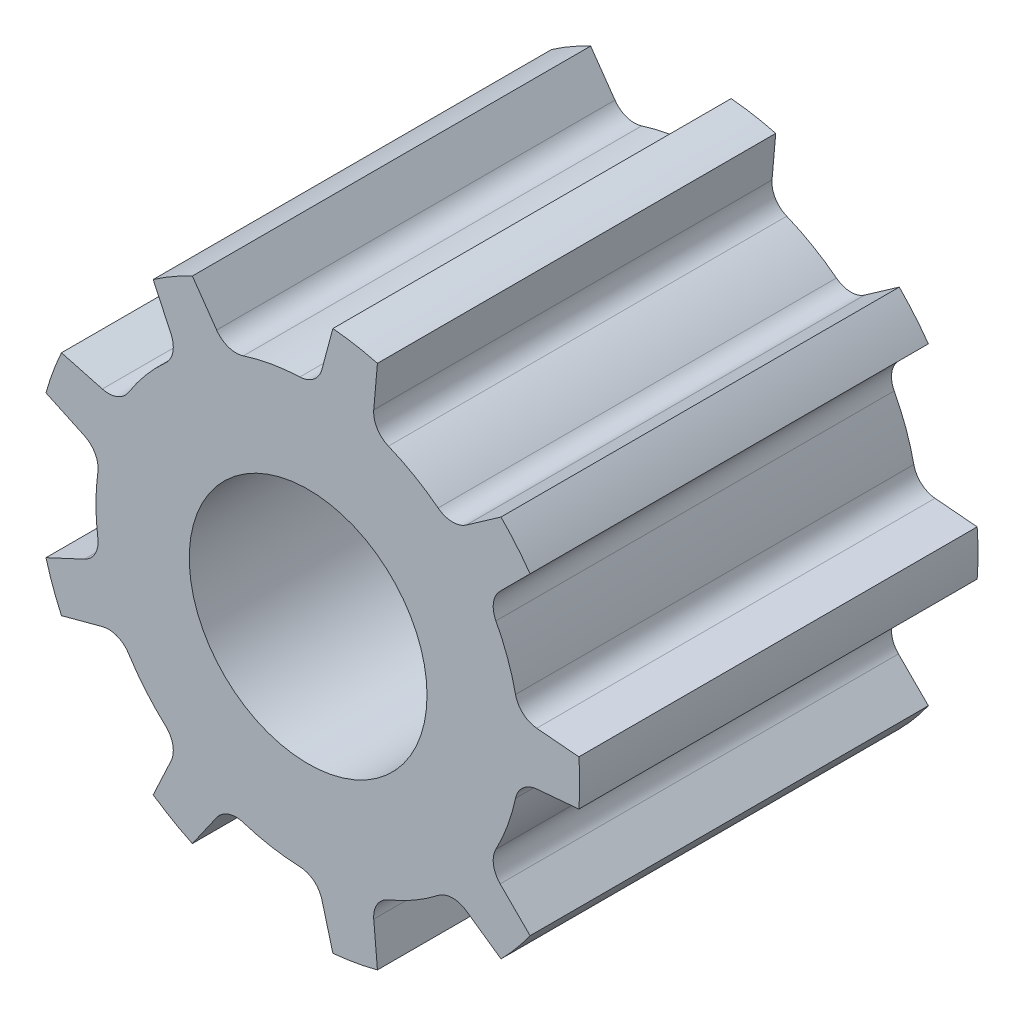
SolidWorks part; units mm, degrees
ref_plane "Front Plane" through (0, 0, 0) normal (0, 0, 1) x (1, 0, 0)
ref_plane "Top Plane" through (0, 0, 0) normal (0, 1, 0) x (1, 0, 0)
ref_plane "Right Plane" through (0, 0, 0) normal (1, 0, 0) x (0, 0, -1)
sketch "Sketch2" plane through (0, 0, 0) normal (0, 0, 1) x (1, 0, 0)
  line L0 (0, 0) -> (-7.1505, 0) construction
  line L1 (-4.4096, -1.2) -> (-3.7645, -0.8992)
  line L2 (-4.4096, 1.2) -> (-3.7645, 0.8992)
  line L3 (-2.6066, 3.7537) -> (-2.3058, 3.1086)
  line L4 (-4.1493, 1.9152) -> (-3.4618, 1.731)
  line L5 (0.416, 4.551) -> (0.2318, 3.8635)
  line L6 (-1.9475, 4.1343) -> (-1.5392, 3.5512)
  line L7 (3.244, 3.2189) -> (2.661, 2.8106)
  line L8 (1.1656, 4.4189) -> (1.1035, 3.7098)
  line L9 (4.5541, 0.3806) -> (3.845, 0.4426)
  line L10 (3.7333, 2.6358) -> (3.23, 2.1325)
  line L11 (3.7333, -2.6358) -> (3.23, -2.1325)
  line L12 (4.5541, -0.3806) -> (3.845, -0.4426)
  line L13 (1.1656, -4.4189) -> (1.1035, -3.7098)
  line L14 (3.244, -3.2189) -> (2.661, -2.8106)
  line L15 (-1.9475, -4.1343) -> (-1.5392, -3.5512)
  line L16 (0.416, -4.551) -> (0.2318, -3.8635)
  line L17 (-4.1493, -1.9152) -> (-3.4618, -1.731)
  line L18 (-2.6066, -3.7537) -> (-2.3058, -3.1086)
  arc A0 (-3.5372, 0.4826) -> (-3.5372, -0.4826) centre (0, 0) ccw
  arc A1 (-4.1493, 1.9152) -> (-4.4096, 1.2) centre (0, 0) ccw construction
  arc A2 (-3.7645, -0.8992) -> (-3.5372, -0.4826) centre (-3.9336, -0.5367) ccw
  arc A3 (-3.7645, 0.8992) -> (-3.5372, 0.4826) centre (-3.9336, 0.5367) cw
  arc A4 (-4.1493, 1.9152) -> (-4.4096, 1.2) centre (0, 0) ccw construction
  arc A5 (-2.3058, 3.1086) -> (-2.3995, 2.6434) centre (-2.6683, 2.9395) cw
  arc A6 (-2.3995, 2.6434) -> (-3.0199, 1.904) centre (0, 0) ccw
  arc A7 (-3.4618, 1.731) -> (-3.0199, 1.904) centre (-3.3582, 2.1173) ccw
  arc A8 (-4.1493, 1.9152) -> (-4.4096, 1.2) centre (0, 0) ccw construction
  arc A9 (0.2318, 3.8635) -> (-0.139, 3.5673) centre (-0.1546, 3.967) cw
  arc A10 (-0.139, 3.5673) -> (-1.0895, 3.3997) centre (0, 0) ccw
  arc A11 (-1.5392, 3.5512) -> (-1.0895, 3.3997) centre (-1.2116, 3.7806) ccw
  arc A12 (-4.1493, 1.9152) -> (-4.4096, 1.2) centre (0, 0) ccw
  arc A13 (2.661, 2.8106) -> (2.1865, 2.822) centre (2.4315, 3.1382) cw
  arc A14 (2.1865, 2.822) -> (1.3507, 3.3046) centre (0, 0) ccw
  arc A15 (1.1035, 3.7098) -> (1.3507, 3.3046) centre (1.502, 3.6749) ccw
  arc A16 (-4.1493, 1.9152) -> (-4.4096, 1.2) centre (0, 0) ccw
  arc A17 (3.845, 0.4426) -> (3.489, 0.7563) centre (3.8799, 0.8411) cw
  arc A18 (3.489, 0.7563) -> (3.1589, 1.6633) centre (0, 0) ccw
  arc A19 (3.23, 2.1325) -> (3.1589, 1.6633) centre (3.5128, 1.8496) ccw
  arc A20 (-4.1493, 1.9152) -> (-4.4096, 1.2) centre (0, 0) ccw
  arc A21 (3.23, -2.1325) -> (3.1589, -1.6633) centre (3.5128, -1.8496) cw
  arc A22 (3.1589, -1.6633) -> (3.489, -0.7563) centre (0, 0) ccw
  arc A23 (3.845, -0.4426) -> (3.489, -0.7563) centre (3.8799, -0.8411) ccw
  arc A24 (-4.1493, 1.9152) -> (-4.4096, 1.2) centre (0, 0) ccw
  arc A25 (1.1035, -3.7098) -> (1.3507, -3.3046) centre (1.502, -3.6749) cw
  arc A26 (1.3507, -3.3046) -> (2.1865, -2.822) centre (0, 0) ccw
  arc A27 (2.661, -2.8106) -> (2.1865, -2.822) centre (2.4315, -3.1382) ccw
  arc A28 (-4.1493, 1.9152) -> (-4.4096, 1.2) centre (0, 0) ccw
  arc A29 (-1.5392, -3.5512) -> (-1.0895, -3.3997) centre (-1.2116, -3.7806) cw
  arc A30 (-1.0895, -3.3997) -> (-0.139, -3.5673) centre (0, 0) ccw
  arc A31 (0.2318, -3.8635) -> (-0.139, -3.5673) centre (-0.1546, -3.967) ccw
  arc A32 (-4.1493, 1.9152) -> (-4.4096, 1.2) centre (0, 0) ccw
  arc A33 (-3.4618, -1.731) -> (-3.0199, -1.904) centre (-3.3582, -2.1173) cw
  arc A34 (-3.0199, -1.904) -> (-2.3995, -2.6434) centre (0, 0) ccw
  arc A35 (-2.3058, -3.1086) -> (-2.3995, -2.6434) centre (-2.6683, -2.9395) ccw
  circle A36 centre (0, 0) radius 2
  arc A37 (-1.9475, 4.1343) -> (-2.6066, 3.7537) centre (0, 0) ccw construction
  arc A38 (-1.9475, 4.1343) -> (-2.6066, 3.7537) centre (0, 0) ccw construction
  arc A39 (-1.9475, 4.1343) -> (-2.6066, 3.7537) centre (0, 0) ccw construction
  arc A40 (-1.9475, 4.1343) -> (-2.6066, 3.7537) centre (0, 0) ccw
  arc A41 (-1.9475, 4.1343) -> (-2.6066, 3.7537) centre (0, 0) ccw
  arc A42 (-1.9475, 4.1343) -> (-2.6066, 3.7537) centre (0, 0) ccw
  arc A43 (-1.9475, 4.1343) -> (-2.6066, 3.7537) centre (0, 0) ccw
  arc A44 (-1.9475, 4.1343) -> (-2.6066, 3.7537) centre (0, 0) ccw
  arc A45 (-1.9475, 4.1343) -> (-2.6066, 3.7537) centre (0, 0) ccw
  arc A46 (-2.6066, -3.7537) -> (-1.9475, -4.1343) centre (0, 0) ccw construction
  arc A47 (-2.6066, -3.7537) -> (-1.9475, -4.1343) centre (0, 0) ccw construction
  arc A48 (-2.6066, -3.7537) -> (-1.9475, -4.1343) centre (0, 0) ccw construction
  arc A49 (-2.6066, -3.7537) -> (-1.9475, -4.1343) centre (0, 0) ccw
  arc A50 (-2.6066, -3.7537) -> (-1.9475, -4.1343) centre (0, 0) ccw
  arc A51 (-2.6066, -3.7537) -> (-1.9475, -4.1343) centre (0, 0) ccw
  arc A52 (-2.6066, -3.7537) -> (-1.9475, -4.1343) centre (0, 0) ccw
  arc A53 (-2.6066, -3.7537) -> (-1.9475, -4.1343) centre (0, 0) ccw
  arc A54 (-2.6066, -3.7537) -> (-1.9475, -4.1343) centre (0, 0) ccw
  arc A55 (0.416, -4.551) -> (1.1656, -4.4189) centre (0, 0) ccw construction
  arc A56 (0.416, -4.551) -> (1.1656, -4.4189) centre (0, 0) ccw construction
  arc A57 (0.416, -4.551) -> (1.1656, -4.4189) centre (0, 0) ccw construction
  arc A58 (0.416, -4.551) -> (1.1656, -4.4189) centre (0, 0) ccw
  arc A59 (0.416, -4.551) -> (1.1656, -4.4189) centre (0, 0) ccw
  arc A60 (0.416, -4.551) -> (1.1656, -4.4189) centre (0, 0) ccw
  arc A61 (0.416, -4.551) -> (1.1656, -4.4189) centre (0, 0) ccw
  arc A62 (0.416, -4.551) -> (1.1656, -4.4189) centre (0, 0) ccw
  arc A63 (0.416, -4.551) -> (1.1656, -4.4189) centre (0, 0) ccw
  arc A64 (3.244, -3.2189) -> (3.7333, -2.6358) centre (0, 0) ccw construction
  arc A65 (3.244, -3.2189) -> (3.7333, -2.6358) centre (0, 0) ccw construction
  arc A66 (3.244, -3.2189) -> (3.7333, -2.6358) centre (0, 0) ccw construction
  arc A67 (3.244, -3.2189) -> (3.7333, -2.6358) centre (0, 0) ccw
  arc A68 (3.244, -3.2189) -> (3.7333, -2.6358) centre (0, 0) ccw
  arc A69 (3.244, -3.2189) -> (3.7333, -2.6358) centre (0, 0) ccw
  arc A70 (3.244, -3.2189) -> (3.7333, -2.6358) centre (0, 0) ccw
  arc A71 (3.244, -3.2189) -> (3.7333, -2.6358) centre (0, 0) ccw
  arc A72 (3.244, -3.2189) -> (3.7333, -2.6358) centre (0, 0) ccw
  arc A73 (4.5541, -0.3806) -> (4.5541, 0.3806) centre (0, 0) ccw construction
  arc A74 (4.5541, -0.3806) -> (4.5541, 0.3806) centre (0, 0) ccw construction
  arc A75 (4.5541, -0.3806) -> (4.5541, 0.3806) centre (0, 0) ccw construction
  arc A76 (4.5541, -0.3806) -> (4.5541, 0.3806) centre (0, 0) ccw
  arc A77 (4.5541, -0.3806) -> (4.5541, 0.3806) centre (0, 0) ccw
  arc A78 (4.5541, -0.3806) -> (4.5541, 0.3806) centre (0, 0) ccw
  arc A79 (4.5541, -0.3806) -> (4.5541, 0.3806) centre (0, 0) ccw
  arc A80 (4.5541, -0.3806) -> (4.5541, 0.3806) centre (0, 0) ccw
  arc A81 (4.5541, -0.3806) -> (4.5541, 0.3806) centre (0, 0) ccw
  arc A82 (3.7333, 2.6358) -> (3.244, 3.2189) centre (0, 0) ccw construction
  arc A83 (3.7333, 2.6358) -> (3.244, 3.2189) centre (0, 0) ccw construction
  arc A84 (3.7333, 2.6358) -> (3.244, 3.2189) centre (0, 0) ccw construction
  arc A85 (3.7333, 2.6358) -> (3.244, 3.2189) centre (0, 0) ccw
  arc A86 (3.7333, 2.6358) -> (3.244, 3.2189) centre (0, 0) ccw
  arc A87 (3.7333, 2.6358) -> (3.244, 3.2189) centre (0, 0) ccw
  arc A88 (3.7333, 2.6358) -> (3.244, 3.2189) centre (0, 0) ccw
  arc A89 (3.7333, 2.6358) -> (3.244, 3.2189) centre (0, 0) ccw
  arc A90 (3.7333, 2.6358) -> (3.244, 3.2189) centre (0, 0) ccw
  arc A91 (1.1656, 4.4189) -> (0.416, 4.551) centre (0, 0) ccw construction
  arc A92 (1.1656, 4.4189) -> (0.416, 4.551) centre (0, 0) ccw construction
  arc A93 (1.1656, 4.4189) -> (0.416, 4.551) centre (0, 0) ccw construction
  arc A94 (1.1656, 4.4189) -> (0.416, 4.551) centre (0, 0) ccw
  arc A95 (1.1656, 4.4189) -> (0.416, 4.551) centre (0, 0) ccw
  arc A96 (1.1656, 4.4189) -> (0.416, 4.551) centre (0, 0) ccw
  arc A97 (1.1656, 4.4189) -> (0.416, 4.551) centre (0, 0) ccw
  arc A98 (1.1656, 4.4189) -> (0.416, 4.551) centre (0, 0) ccw
  arc A99 (1.1656, 4.4189) -> (0.416, 4.551) centre (0, 0) ccw
  arc A100 (-4.4096, -1.2) -> (-4.1493, -1.9152) centre (0, 0) ccw construction
  arc A101 (-4.4096, -1.2) -> (-4.1493, -1.9152) centre (0, 0) ccw construction
  arc A102 (-4.4096, -1.2) -> (-4.1493, -1.9152) centre (0, 0) ccw construction
  arc A103 (-4.4096, -1.2) -> (-4.1493, -1.9152) centre (0, 0) ccw
  arc A104 (-4.4096, -1.2) -> (-4.1493, -1.9152) centre (0, 0) ccw
  arc A105 (-4.4096, -1.2) -> (-4.1493, -1.9152) centre (0, 0) ccw
  arc A106 (-4.4096, -1.2) -> (-4.1493, -1.9152) centre (0, 0) ccw
  arc A107 (-4.4096, -1.2) -> (-4.1493, -1.9152) centre (0, 0) ccw
  arc A108 (-4.4096, -1.2) -> (-4.1493, -1.9152) centre (0, 0) ccw
  point P86 (0, 0)
  dimension "D1" = 7.14
  dimension "D2" = 9.14
  dimension "D5" = 0.4
  dimension "D7" = 4
  dimension "D3" = 25
  dimension "D4" = 1.2
  dimension "D6" = 9
extrude "Boss-Extrude1" add sketch "Sketch2" along normal blind 6.7 contours L1 A103 L17 A33 A34 A35 L18 A49 L15 A29 A30 A31 L16 A58 L13 A25 A26 A27 L14 A67 L11 A21 A22 A23 L12 A76 L9 A17 A18 A19 L10 A85 L7 A13 A14 A15 L8 A94 L5 A9 A10 A11 L6 A40 L3 A5 A6 A7 L4 A12 L2
